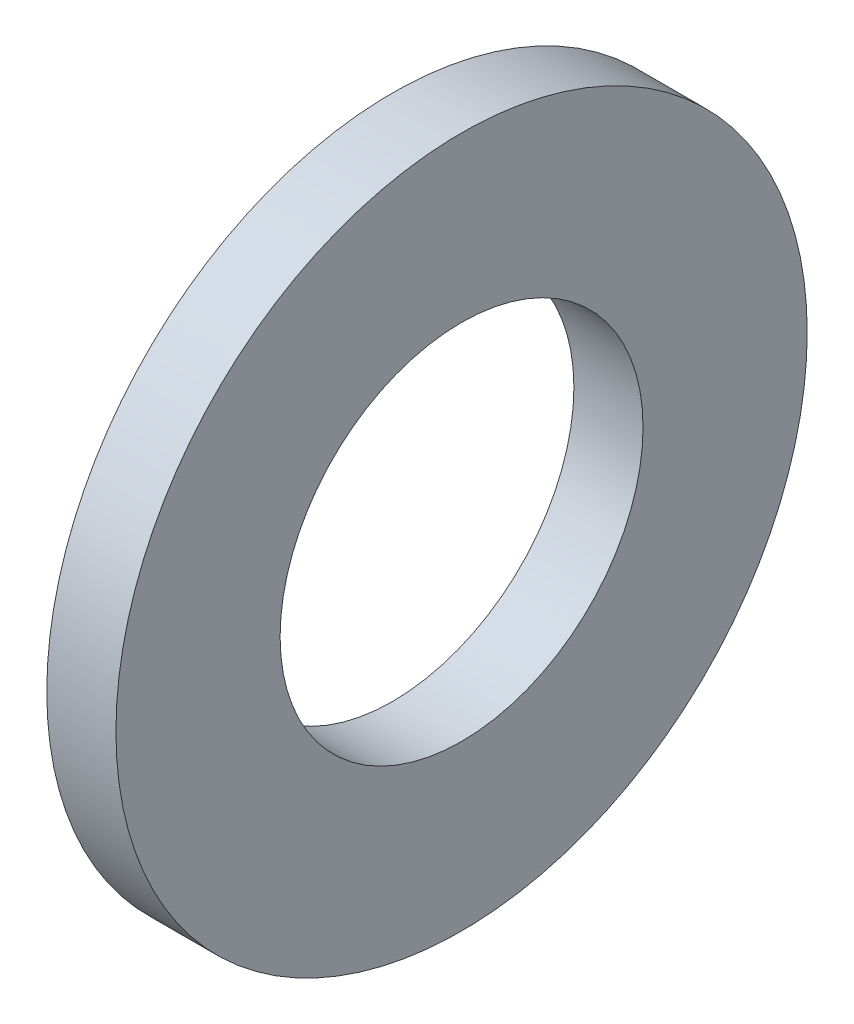
SolidWorks part; units mm, degrees
ref_plane "Płaszczyzna przednia" through (0, 0, 0) normal (0, 0, 1) x (1, 0, 0)
ref_plane "Płaszczyzna górna" through (0, 0, 0) normal (0, 1, 0) x (1, 0, 0)
ref_plane "Płaszczyzna prawa" through (0, 0, 0) normal (1, 0, 0) x (0, 0, -1)
sketch "Szkic1" plane through (0, 0, 0) normal (0, 0, 1) x (1, 0, 0)
  line L0 (4.7156, 10) -> (4.7156, 5.25)
  line L1 (4.7156, 5.25) -> (6.7156, 5.25)
  line L2 (6.7156, 5.25) -> (6.7156, 10)
  line L3 (6.7156, 10) -> (4.7156, 10)
  line L4 (0, 0) -> (3, 0) construction
  dimension "D1" = 5.25
  dimension "D2" = 2
  dimension "D3" = 10
  dimension "D4" = 3
  dimension "D5" = 4.7156
revolve "Obrót1" add sketch "Szkic1" angle 360 about L4
